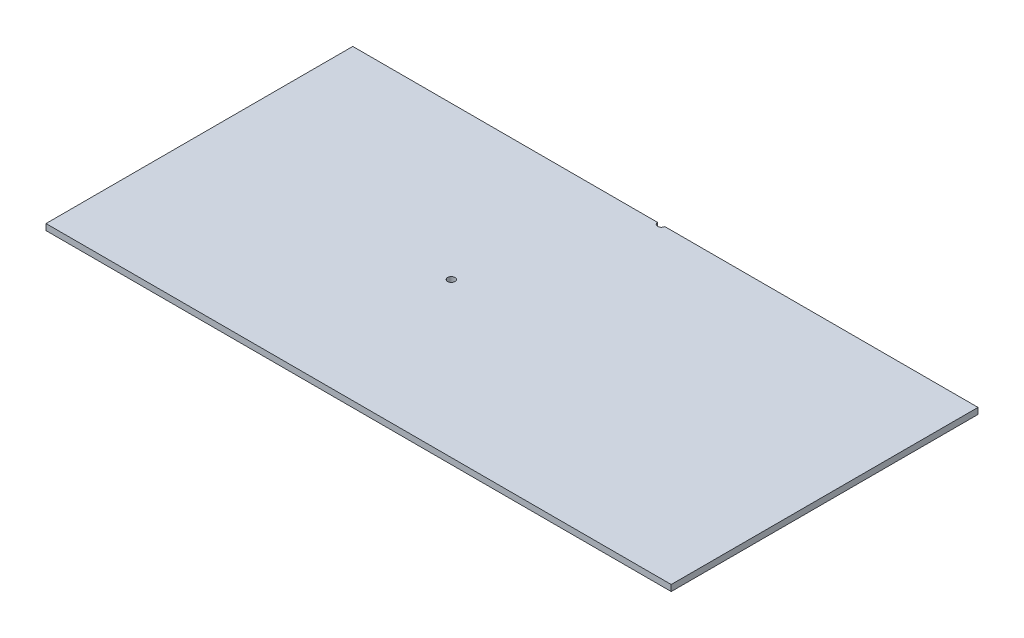
SolidWorks part; units mm, degrees
ref_plane "Front Plane" through (0, 0, 0) normal (0, 0, 1) x (1, 0, 0)
ref_plane "Top Plane" through (0, 0, 0) normal (0, 1, 0) x (1, 0, 0)
ref_plane "Right Plane" through (0, 0, 0) normal (1, 0, 0) x (0, 0, -1)
sketch "Sketch1" plane through (0, 0, 0) normal (0, 1, 0) x (1, 0, 0)
  line L1 (-117.7125, 60.0612) -> (140.6989, 60.0612)
  line L2 (-117.7125, 60.0612) -> (-117.7125, -66.7346)
  line L3 (-117.7125, -66.7346) -> (140.6989, -66.7346)
  line L4 (140.6989, 60.0612) -> (140.6989, -66.7346)
extrude "Boss-Extrude1" add sketch "Sketch1" along normal blind 2.54
hole_wizard "Ø3.0 (3) Diameter Hole1" positions "Sketch3" profile "Sketch2" hole size "Ø3.0" standard "Ansi Metric"
sketch "Sketch3" plane through (0, 2.54, 0) normal (0, 1, 0) x (-1, 0, 0)
  circle A0 centre (13.9247, 3.0108) radius 1.5 construction
  point P0 (13.9247, 3.0108)
  dimension "D1" = 0
  dimension "D2" = 0
sketch "Sketch2" plane through (-13.9247, 2.54, 3.0108) normal (1, 0, 0) x (0, 0, 1)
  line L0 (0, 0) -> (0, 26.3013)
  line L1 (0, 26.3013) -> (1.5, 25.4)
  line L2 (1.5, 25.4) -> (1.5, 0)
  line L5 (1.5, 0) -> (0, 0)
  line L10 (0, 26.3013) -> (-1.5, 25.4) construction
  line L11 (0, -6.35) -> (0, 107.95) construction
  dimension "Hole Dia." = 3
  dimension "Hole Depth" = 25.4
  dimension "Drill Angle" = 118
hole_wizard "Ø3.0 (3) Diameter Hole2" positions "Sketch7" profile "Sketch6" hole size "Ø3.0" standard "Ansi Metric"
sketch "Sketch7" plane through (0, 0, 0) normal (0, -1, 0) x (1, 0, 0)
  ellipse E0 centre (9.7404, -60.1357) end of major axis (12.4157, -62.1929) minor radius 2.2001 construction
  point P0 (9.7404, -60.1357)
  dimension "D1" = 0
sketch "Sketch6" plane through (9.7404, 0, -60.1357) normal (1, 0, 0) x (0, 0, -1)
  line L0 (0, 0) -> (0, 26.3013)
  line L1 (0, 26.3013) -> (1.5, 25.4)
  line L2 (1.5, 25.4) -> (1.5, 0)
  line L5 (1.5, 0) -> (0, 0)
  line L10 (0, 26.3013) -> (-1.5, 25.4) construction
  line L11 (0, -6.35) -> (0, 107.95) construction
  dimension "Hole Dia." = 3
  dimension "Hole Depth" = 25.4
  dimension "Drill Angle" = 118
